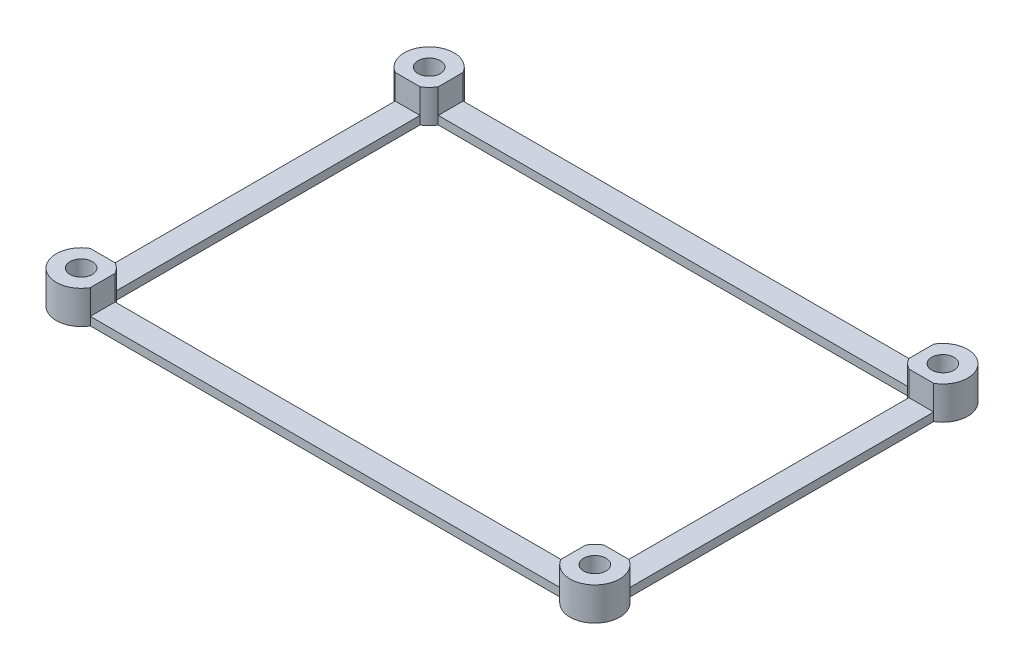
SolidWorks part; units mm, degrees
ref_plane "Front Plane" through (0, 0, 0) normal (0, 0, 1) x (1, 0, 0)
ref_plane "Top Plane" through (0, 0, 0) normal (0, 1, 0) x (1, 0, 0)
ref_plane "Right Plane" through (0, 0, 0) normal (1, 0, 0) x (0, 0, -1)
sketch "Sketch1" plane through (0, 0, 0) normal (0, 1, 0) x (1, 0, 0)
  line L1 (-31, -21) -> (31, -21) construction
  line L2 (-31, -21) -> (-31, 21) construction
  line L3 (-31, 21) -> (31, 21) construction
  line L4 (31, -21) -> (31, 21) construction
  line L5 (-31, -21) -> (31, 21) construction
  line L6 (-31, 21) -> (31, -21) construction
  line L7 (-28.4019, 19.5) -> (28.4019, 19.5)
  line L9 (-28.4019, 22.5) -> (28.4019, 22.5)
  line L11 (-28.4019, 19.5) -> (28.4019, 22.5) construction
  line L12 (-28.4019, 22.5) -> (28.4019, 19.5) construction
  line L14 (-32.5, -18.4019) -> (-32.5, 18.4019)
  line L16 (-29.5, -18.4019) -> (-29.5, 18.4019)
  line L17 (-32.5, -18.4019) -> (-29.5, 18.4019) construction
  line L18 (-32.5, 18.4019) -> (-29.5, -18.4019) construction
  line L20 (29.5, -18.4019) -> (29.5, 18.4019)
  line L22 (32.5, -18.4019) -> (32.5, 18.4019)
  line L23 (29.5, -18.4019) -> (32.5, 18.4019) construction
  line L24 (29.5, 18.4019) -> (32.5, -18.4019) construction
  line L25 (-28.4019, -22.5) -> (28.4019, -22.5)
  line L27 (-28.4019, -19.5) -> (28.4019, -19.5)
  line L29 (-28.4019, -22.5) -> (28.4019, -19.5) construction
  line L30 (-28.4019, -19.5) -> (28.4019, -22.5) construction
  circle A0 centre (31, 21) radius 1.35
  circle A1 centre (31, -21) radius 1.35
  circle A2 centre (-31, -21) radius 1.35
  circle A3 centre (-31, 21) radius 1.35
  arc A4 (-29.5, 18.4019) -> (-28.4019, 19.5) centre (-31, 21) ccw
  arc A5 (28.4019, 19.5) -> (29.5, 18.4019) centre (31, 21) ccw
  arc A6 (29.5, -18.4019) -> (28.4019, -19.5) centre (31, -21) ccw
  arc A7 (-28.4019, -19.5) -> (-29.5, -18.4019) centre (-31, -21) ccw
  arc A8 (-32.5, -18.4019) -> (-28.4019, -22.5) centre (-31, -21) ccw
  arc A9 (-28.4019, 22.5) -> (-32.5, 18.4019) centre (-31, 21) ccw
  arc A10 (32.5, 18.4019) -> (28.4019, 22.5) centre (31, 21) ccw
  arc A11 (28.4019, -22.5) -> (32.5, -18.4019) centre (31, -21) ccw
  point P0 (0, 0)
  point P10 (-28.4019, -19.24)
  point P14 (0, 21)
  point P19 (-31, 0)
  point P24 (31, 0)
  point P29 (0, -21)
  dimension "D3" = 2.7
  dimension "D4" = 6
  dimension "D1" = 62
  dimension "D2" = 42
  dimension "D5" = 3
  dimension "D6" = 3
  dimension "D7" = 3
  dimension "D8" = 3
extrude "Boss-Extrude1" add sketch "Sketch1" along normal blind 4
sketch "Sketch2" plane through (0, 4, 0) normal (0, 1, 0) x (1, 0, 0)
  line L1 (-32.5, 18.4019) -> (-29.5, 18.4019)
  line L2 (-32.5, 18.4019) -> (-32.5, -18.4019)
  line L3 (-32.5, -18.4019) -> (-29.5, -18.4019)
  line L4 (-29.5, 18.4019) -> (-29.5, -18.4019)
  line L5 (-28.4019, -19.5) -> (28.4019, -19.5)
  line L6 (-28.4019, -19.5) -> (-28.4019, -22.5)
  line L7 (-28.4019, -22.5) -> (28.4019, -22.5)
  line L8 (28.4019, -19.5) -> (28.4019, -22.5)
  line L9 (29.5, -18.4019) -> (32.5, -18.4019)
  line L10 (29.5, -18.4019) -> (29.5, 18.4019)
  line L11 (29.5, 18.4019) -> (32.5, 18.4019)
  line L12 (32.5, -18.4019) -> (32.5, 18.4019)
  line L13 (28.4019, 19.5) -> (-28.4019, 19.5)
  line L14 (28.4019, 19.5) -> (28.4019, 22.5)
  line L15 (28.4019, 22.5) -> (-28.4019, 22.5)
  line L16 (-28.4019, 19.5) -> (-28.4019, 22.5)
extrude "Cut-Extrude1" cut sketch "Sketch2" against normal offset from surface (3 mm away) 1 up to face at (-31, 0, -19.65)
